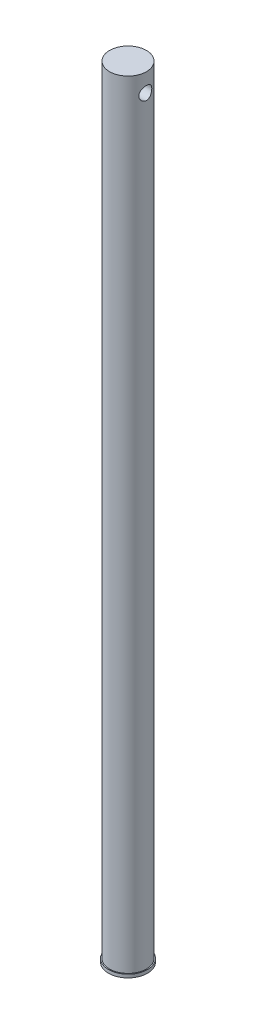
SolidWorks part; units mm, degrees
ref_plane "Front Plane" through (0, 0, 0) normal (0, 0, 1) x (1, 0, 0)
ref_plane "Top Plane" through (0, 0, 0) normal (0, 1, 0) x (1, 0, 0)
ref_plane "Right Plane" through (0, 0, 0) normal (1, 0, 0) x (0, 0, -1)
sketch "Sketch2" plane through (0, 0, 0) normal (0, 1, 0) x (1, 0, 0)
  circle A0 centre (0, 0) radius 9
  dimension "D1" = 18
extrude "Boss-Extrude1" add sketch "Sketch2" along normal blind 381
sketch "Sketch3" plane through (0, 0, 0) normal (0, -1, 0) x (1, 0, 0)
  circle A0 centre (0, 0) radius 9.5
  dimension "D1" = 19
extrude "Boss-Extrude2" add sketch "Sketch3" against normal blind 1.5875
sketch "Sketch4" plane through (0, 0, 0) normal (1, 0, 0) x (0, 0, -1)
  line L0 (9, 381) -> (-9, 381) construction
  line L1 (0, 0) -> (0, 372) construction
  circle A0 centre (0, 372) radius 3.175
  dimension "D1" = 6.35
  dimension "D2" = 9
extrude "Cut-Extrude1" cut sketch "Sketch4" against normal through all and the other way through all
